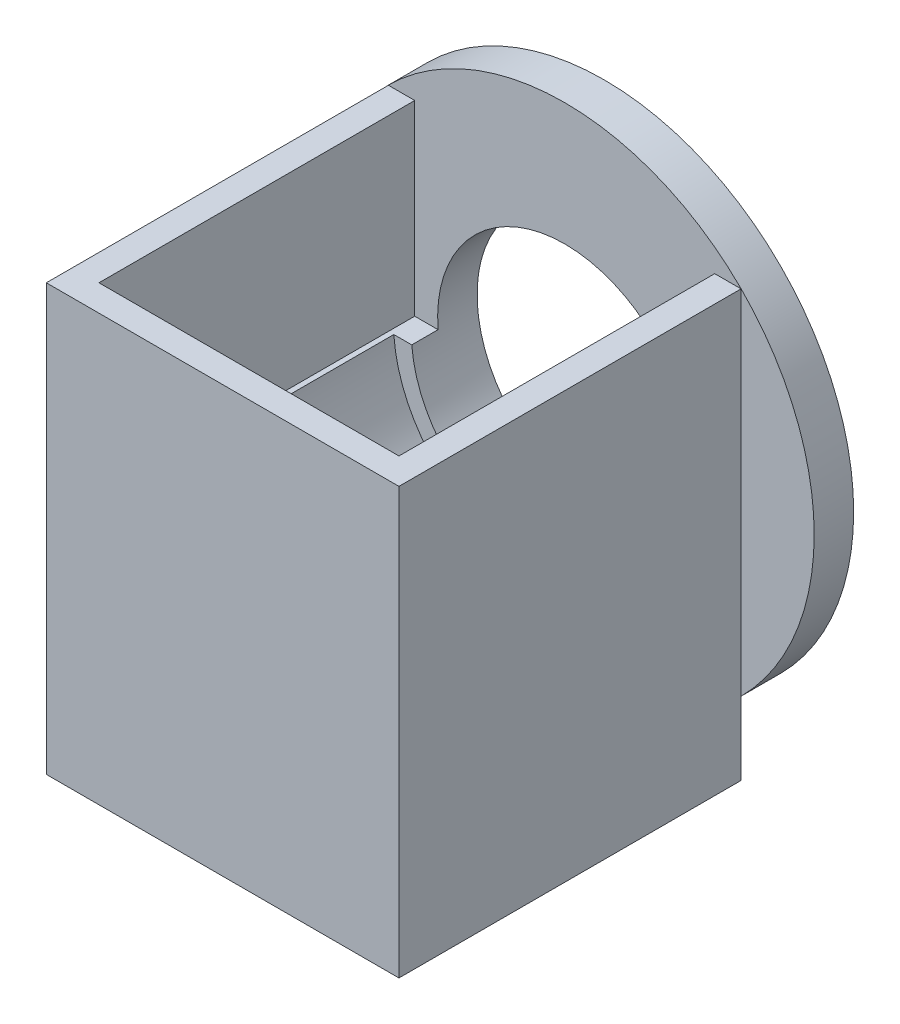
SolidWorks part; units mm, degrees
ref_plane "Front Plane" through (0, 0, 0) normal (0, 0, 1) x (1, 0, 0)
ref_plane "Top Plane" through (0, 0, 0) normal (0, 1, 0) x (1, 0, 0)
ref_plane "Right Plane" through (0, 0, 0) normal (1, 0, 0) x (0, 0, -1)
sketch "Sketch3" plane through (0, 0, 0) normal (0, 0, 1) x (1, 0, 0)
  circle A0 centre (0, 0) radius 47.4
  dimension "D1" = 94.8
extrude "Boss-Extrude2" add sketch "Sketch3" along normal blind 7.5
sketch "Sketch4" plane through (0, 0, 7.5) normal (0, 0, 1) x (1, 0, 0)
  circle A0 centre (0, 0) radius 24.15
  dimension "D1" = 48.3
extrude "Cut-Extrude1" cut sketch "Sketch4" against normal blind 15
sketch "Sketch5" plane through (0, 0, 7.5) normal (0, 0, 1) x (1, 0, 0)
  line L0 (0, 0) -> (0, -21.9707) construction
  line L1 (-33.5, -47.4) -> (33.5, -47.4)
  line L2 (-33.5, -47.4) -> (-33.5, -33.5)
  line L4 (33.5, -47.4) -> (33.5, -33.5)
  line L5 (-33.5, -47.4) -> (33.5, 33.5) construction
  line L6 (-33.5, 33.5) -> (33.5, -47.4) construction
  line L7 (0, 24.15) -> (0, 33.5) construction
  line L10 (-33.5, -33.5) -> (33.5, -33.5) construction
  line L12 (0, -24.15) -> (0, -33.5) construction
  line L13 (33.5, -33.5) -> (33.5, 33.5)
  line L14 (-33.5, 33.5) -> (0, 33.5)
  line L15 (0, 33.5) -> (33.5, 33.5)
  line L16 (-33.5, -33.5) -> (-33.5, 33.5)
  circle A0 centre (0, 0) radius 47.4 construction
  circle A2 centre (0, 0) radius 24.15 construction
  point P0 (0, -6.95)
  dimension "D1" = 67
extrude "Boss-Extrude4" add sketch "Sketch5" along normal blind 65
sketch "Sketch6" plane through (0, 0, 7.5) normal (0, 0, -1) x (-1, 0, 0)
  circle A0 centre (0, 0) radius 24.15
extrude "Cut-Extrude2" cut sketch "Sketch6" against normal blind 5
sketch "Sketch7" plane through (0, 33.5, 0) normal (0, 1, 0) x (1, 0, 0)
  line L0 (-47.4, -7.5) -> (47.4, -7.5) construction
  line L1 (-28.5, -7.5) -> (28.5, -7.5)
  line L2 (-28.5, -7.5) -> (-28.5, -67.5)
  line L3 (-28.5, -67.5) -> (28.5, -67.5)
  line L4 (28.5, -7.5) -> (28.5, -67.5)
  line L5 (0, -67.5) -> (0, -72.5) construction
  line L6 (33.5, -72.5) -> (-33.5, -72.5) construction
  point P10 (0, 0)
  dimension "D1" = 60
  dimension "D2" = 57
extrude "Cut-Extrude3" cut sketch "Sketch7" against normal blind 35.5
sketch "Sketch8" plane through (0, 0, 12.5) normal (0, 0, -1) x (-1, 0, 0)
  circle A0 centre (0, 0) radius 27.55
  dimension "D1" = 55.1
extrude "Cut-Extrude4" cut sketch "Sketch8" against normal up to surface (55 mm away) up to face at (0, 15.75, 67.5)
